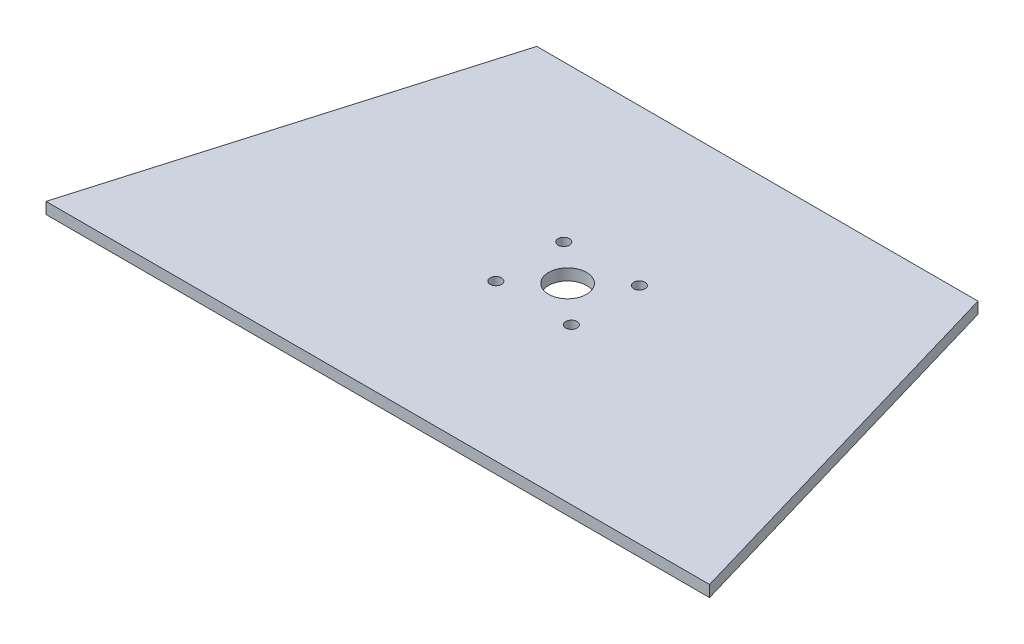
SolidWorks part; units mm, degrees
ref_plane "Front Plane" through (0, 0, 0) normal (0, 0, 1) x (1, 0, 0)
ref_plane "Top Plane" through (0, 0, 0) normal (0, 1, 0) x (1, 0, 0)
ref_plane "Right Plane" through (0, 0, 0) normal (1, 0, 0) x (0, 0, -1)
sketch "Sketch1" plane through (0, 0, 0) normal (0, 1, 0) x (1, 0, 0)
  line L0 (5.2, 0) -> (180, 0)
  line L3 (90, 0) -> (90, 100) construction
  line L5 (5.2, 0) -> (34.4799, 100)
  line L6 (180, 0) -> (150.7201, 100)
  line L7 (34.4799, 100) -> (150.7201, 100)
extrude "Boss-Extrude1" add sketch "Sketch1" along normal blind 3
hole_wizard "Ø3.0mm Dowel Hole1" positions "Sketch2" profile "Sketch3" hole size "Ø3.0" standard "ANSI Metric" end condition up to next
sketch "Sketch2" plane through (0, 0, 0) normal (0, -1, 0) x (-1, 0, 0)
  point P0 (-82.65, 58.95)
  point P3 (-82.65, 41.05)
  point P6 (-102.55, 41.05)
  point P9 (-102.55, 58.95)
sketch "Sketch3" plane through (82.65, 0, -58.95) normal (1, 0, 0) x (0, 0, -1)
  line L0 (0, 0) -> (0, 3)
  line L1 (0, 3) -> (1.5, 3)
  line L2 (1.5, 3) -> (1.5, 0)
  line L5 (1.5, 0) -> (0, 0)
  line L11 (0, -6.35) -> (0, 107.95) construction
  dimension "Thru Hole Dia." = 3
  dimension "Thru Hole Depth" = 3
hole_wizard "Ø10.0mm Dowel Hole1" positions "Sketch6" profile "Sketch7" hole size "Ø10.0" standard "ANSI Metric" end condition up to next
sketch "Sketch6" plane through (0, 3, 0) normal (0, 1, 0) x (1, 0, 0)
  point P0 (92.6, 50)
sketch "Sketch7" plane through (92.6, 3, -50) normal (1, 0, 0) x (0, 0, 1)
  line L0 (0, 0) -> (0, 3)
  line L1 (0, 3) -> (5, 3)
  line L2 (5, 3) -> (5, 0)
  line L5 (5, 0) -> (0, 0)
  line L11 (0, -6.35) -> (0, 107.95) construction
  dimension "Thru Hole Dia." = 10
  dimension "Thru Hole Depth" = 3
